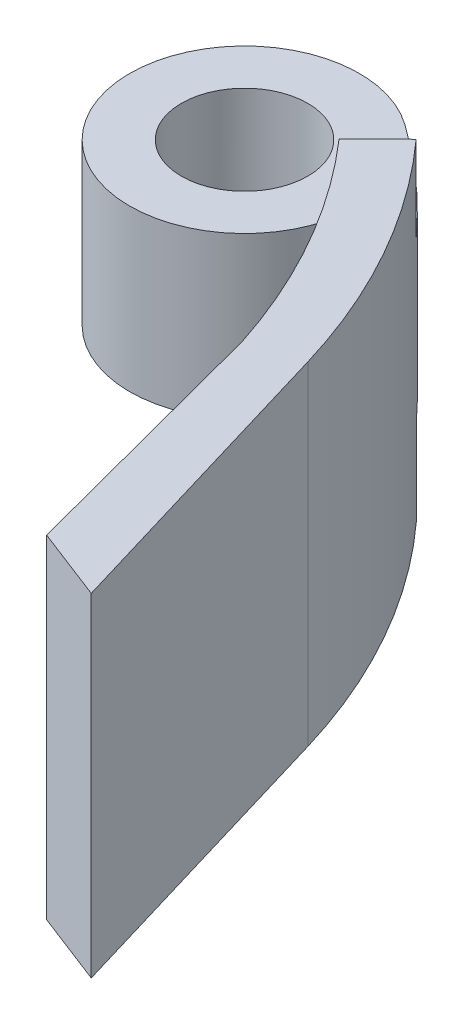
SolidWorks part; units mm, degrees
ref_plane "Front Plane" through (0, 0, 0) normal (0, 0, 1) x (1, 0, 0)
ref_plane "Top Plane" through (0, 0, 0) normal (0, 1, 0) x (1, 0, 0)
ref_plane "Right Plane" through (0, 0, 0) normal (1, 0, 0) x (0, 0, -1)
sketch "Sketch2" plane through (0, 0, 0) normal (0, 1, 0) x (1, 0, 0)
  line L0 (28.8185, 70.9167) -> (26.2959, 67.1881)
  line L1 (50.0098, 41.3112) -> (58.0453, 14.3988)
  line L2 (50.0098, 41.3112) -> (45.6189, 40.0002)
  line L3 (45.6189, 40.0002) -> (51.7108, 16.8486)
  line L4 (51.7108, 16.8486) -> (58.0453, 14.3988)
  arc A0 (45.6189, 40.0002) -> (26.2959, 67.1881) centre (-7.6173, 22.6247) ccw
  arc A2 (50.0098, 41.3112) -> (28.8185, 70.9167) centre (-3.6494, 25.2896) ccw
  circle A3 centre (23.0207, 62.769) radius 10
  circle A4 centre (23.0207, 62.769) radius 5.5
extrude "Boss-Extrude1" add sketch "Sketch2" along normal blind 29 contours A0 A4 L0 A3 | A0 A3 L0 | A3 A0 L2 A2 | L3 L4 L1 L2
ref_plane "Plane1" through (0, 7, 0) normal (0, -1, 0) x (-1, 0, 0)
sketch "Sketch3" plane through (0, 7, 0) normal (0, -1, 0) x (-1, 0, 0)
  line L0 (-39.4573, 64.639) -> (-16.5366, 40.9533)
  line L1 (-39.4573, 64.639) -> (-23.9402, 82.938)
  line L2 (-16.5366, 40.9533) -> (-1.0195, 59.2523)
  line L3 (-23.9402, 82.938) -> (-1.0195, 59.2523)
  circle A0 centre (-23.0207, 62.769) radius 12
ref_plane "Plane3" through (0, 22, 0) normal (0, 1, 0) x (1, 0, 0)
sketch "Sketch6" plane through (0, 22, 0) normal (0, 1, 0) x (1, 0, 0)
  line L0 (38.6188, 63.433) -> (15.1938, 40.271)
  line L1 (38.6188, 63.433) -> (27.0273, 87.0623)
  line L2 (15.1938, 40.271) -> (3.6023, 63.9003)
  line L3 (27.0273, 87.0623) -> (3.6023, 63.9003)
  circle A0 centre (23.0207, 62.769) radius 12
extrude "Cut-Extrude5" cut sketch "Sketch3" against normal blind 0.5 and the other way blind 7 contours A0 L0 L2 L3 L1 | L0 A0 | L0 A0
extrude "Cut-Extrude6" cut sketch "Sketch6" against normal blind 0.5 and the other way blind 7 contours A0 L0 L1 L3 L2 | L0 A0 | L0 A0
ref_plane "Plane4" through (52.5086, 0, -13.8167) normal (-0.9671, 0, 0.2545) x (0.2545, 0, 0.9671)
sketch "Sketch8" plane through (52.5086, 0, -13.8167) normal (-0.9671, 0, 0.2545) x (0.2545, 0, 0.9671)
  line L0 (-15.269, 30.3633) -> (-15.269, -0.8486)
ref_plane "Plane5" through (0, 14.5, 0) normal (0, 1, 0) x (1, 0, 0)
sketch "Sketch9" plane through (0, 14.5, 0) normal (0, 1, 0) x (1, 0, 0)
  circle A0 centre (48.6882, 28.6211) radius 4
  circle A1 centre (48.6882, 28.6211) radius 2
extrude "Boss-Extrude2" add sketch "Sketch9" along normal blind 1 and the other way blind 1
